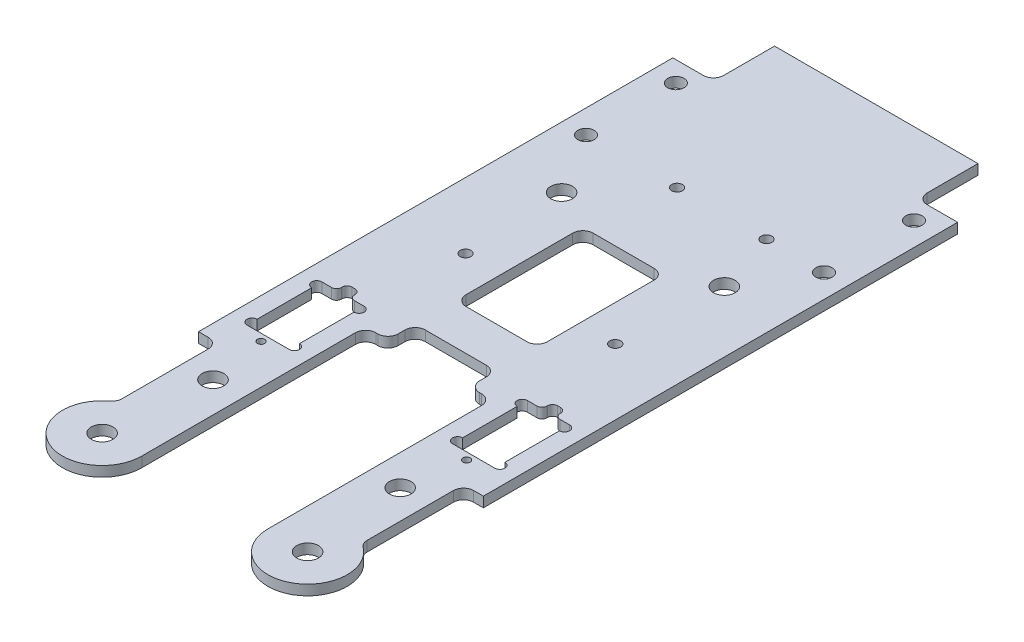
SolidWorks part; units mm, degrees
material "6061-T4 (SS)"
ref_plane "Front Plane" through (0, 0, 0) normal (0, 0, 1) x (1, 0, 0)
ref_plane "Top Plane" through (0, 0, 0) normal (0, 1, 0) x (1, 0, 0)
ref_plane "Right Plane" through (0, 0, 0) normal (1, 0, 0) x (0, 0, -1)
sketch "Sketch1" plane through (0, 0, 0) normal (0, 1, 0) x (1, 0, 0)
  line L1 (-44.45, -114.3) -> (44.45, -114.3)
  line L2 (-44.45, -114.3) -> (-44.45, 114.3)
  line L3 (-44.45, 114.3) -> (44.45, 114.3)
  line L4 (44.45, -114.3) -> (44.45, 114.3)
  line L5 (-44.45, -114.3) -> (44.45, 114.3) construction
  line L6 (-44.45, 114.3) -> (44.45, -114.3) construction
  point P0 (0, 0)
  dimension "D1" = 88.9
  dimension "D2" = 228.6
extrude "Boss-Extrude1" add sketch "Sketch1" along normal blind 3.175
sketch "Sketch11" plane through (0, 3.175, 0) normal (0, 1, 0) x (1, 0, 0)
  line L0 (0, 31.75) -> (97.4414, 31.75) construction
  line L10 (0, 0) -> (0, 114.3) construction
  line L14 (44.45, 114.3) -> (-44.45, 114.3) construction
  line L15 (0, 0) -> (117.475, 0) construction
  circle A0 centre (-26.289, 4.9828) radius 1.25
  circle A1 centre (-25.019, 53.1832) radius 1.25
  circle A2 centre (25.781, 38.1972) radius 1.25
  circle A3 centre (25.781, 10.0628) radius 1.25
  dimension "D3" = 2.5
  dimension "D5" = 2.5
  dimension "D7" = 31.75
  dimension "D9" = 25.781
  dimension "D4" = 2.5
  dimension "D6" = 2.5
  dimension "D2" = 25.019
  dimension "D8" = 26.289
  dimension "D10" = 6.4472
  dimension "D11" = 25.781
  dimension "D12" = 21.6872
  dimension "D13" = 26.7672
  dimension "D14" = 21.4332
extrude "Cut-Extrude12" [suppressed] cut sketch "Sketch11" against normal through all
sketch "Sketch18" plane through (0, 3.175, 0) normal (0, 1, 0) x (1, 0, 0)
  line L0 (44.45, 79.883) -> (-44.45, 79.883) construction
  line L1 (44.45, -114.3) -> (44.45, 114.3) construction
  line L2 (-44.45, 114.3) -> (-44.45, -114.3) construction
  line L3 (44.45, 114.3) -> (-44.45, 114.3) construction
  line L4 (0, 79.883) -> (0, -114.3) construction
  line L5 (-44.45, -114.3) -> (44.45, -114.3) construction
  circle A9 centre (-23.9014, 29.083) radius 1.6891
  circle A10 centre (23.9014, 27.9832) radius 1.6891
  circle A11 centre (-8.702, 79.883) radius 1.6891
  circle A12 centre (19.1999, 79.883) radius 1.6891
  dimension "D4" = 50.8
  dimension "D9" = 15.1994
  dimension "D11" = 3.3782
  dimension "D13" = 43.1013
  dimension "D3" = 3.3782
  dimension "D2" = 3.3782
  dimension "D8" = 3.3782
  dimension "D1" = 34.417
  dimension "D5" = 23.9014
  dimension "D6" = 47.8028
  dimension "D7" = 1.0998
  dimension "D10" = 50.8
  dimension "D12" = 50.8
sketch "Sketch12" plane through (0, 3.175, 0) normal (0, 1, 0) x (1, 0, 0)
  line L0 (0, 0) -> (44.45, 0) construction
  line L1 (44.45, -114.3) -> (44.45, 114.3) construction
  line L2 (0, 0) -> (0, 114.3) construction
  line L3 (44.45, 114.3) -> (-44.45, 114.3) construction
  line L4 (44.45, -44.45) -> (-44.45, -44.45) construction
  line L5 (-19.685, -69.85) -> (19.685, -69.85)
  line L6 (-19.685, -69.85) -> (-19.685, -6.35)
  line L7 (-19.685, -6.35) -> (19.685, -6.35)
  line L8 (19.685, -69.85) -> (19.685, -6.35)
  line L9 (-19.685, -69.85) -> (19.685, -6.35) construction
  line L10 (-19.685, -6.35) -> (19.685, -69.85) construction
  line L11 (-44.45, 114.3) -> (-44.45, -114.3) construction
  line L12 (0, -38.1) -> (0, -114.3) construction
  line L13 (-44.45, -114.3) -> (44.45, -114.3) construction
  circle A0 centre (29.21, -44.45) radius 3.3782
  circle A1 centre (-29.21, -44.45) radius 3.3782
  point P5 (0, -38.1)
  dimension "D5" = 6.7564
  dimension "D1" = 63.5
  dimension "D2" = 38.1
  dimension "D3" = 39.37
  dimension "D4" = 25.4
  dimension "D6" = 58.42
extrude "Cut-Extrude13" cut sketch "Sketch12" against normal through all
sketch "Sketch14" plane through (0, 0, 0) normal (0, -1, 0) x (-1, 0, 0)
  line L0 (0, 114.3) -> (0, 31.056) construction
  line L1 (-44.45, 114.3) -> (44.45, 114.3) construction
  line L2 (0, 114.3) -> (-44.45, 114.3) construction
  line L3 (-41.91, 114.3) -> (-41.91, 67.4804) construction
  line L5 (-32.385, 114.3) -> (-32.385, 67.4804) construction
  line L6 (-32.385, 107.95) -> (-41.91, 107.95) construction
  line L7 (-32.385, 93.9165) -> (-41.91, 93.9165) construction
  line L8 (-44.45, -114.3) -> (-44.45, 114.3) construction
  circle A0 centre (-37.1475, 107.95) radius 2.5527
  circle A1 centre (-37.1475, 79.883) radius 2.5527
  circle A2 centre (37.1475, 107.95) radius 2.5527
  circle A3 centre (37.1475, 79.883) radius 2.5527
  dimension "D4" = 5.1054
  dimension "D1" = 2.54
  dimension "D2" = 9.525
  dimension "D3" = 6.35
  dimension "D5" = 14.0335
extrude "Cut-Extrude15" cut sketch "Sketch14" against normal through all
sketch "Sketch15" plane through (0, 0, 0) normal (0, -1, 0) x (1, 0, 0)
  line L0 (44.45, 114.3) -> (44.45, -114.3) construction
  line L1 (-44.45, 114.3) -> (44.45, 114.3)
  line L2 (-44.45, 114.3) -> (-44.45, 57.15)
  line L3 (-44.45, 57.15) -> (44.45, 57.15)
  line L4 (44.45, 114.3) -> (44.45, 57.15)
  line L5 (19.685, 6.35) -> (-19.685, 6.35) construction
  line L6 (0, -24.0665) -> (0, -114.3) construction
  line L7 (12.7, -51.308) -> (12.7, -17.9917)
  line L8 (9.525, -14.8167) -> (-9.525, -14.8167)
  line L9 (44.45, -114.3) -> (-44.45, -114.3) construction
  line L10 (-12.7, -17.9917) -> (-12.7, -51.308)
  line L11 (9.525, -54.483) -> (-9.525, -54.483)
  line L12 (12.7, -51.308) -> (12.7, 6.35) construction
  line L13 (12.7, 6.35) -> (-12.7, 6.35) construction
  line L14 (-12.7, -51.308) -> (-12.7, 6.35) construction
  line L15 (12.7, -54.483) -> (-12.7, 6.35) construction
  line L16 (12.7, 6.35) -> (-12.7, -54.483) construction
  line L17 (12.7, 6.35) -> (-12.7, 6.35)
  line L18 (-12.7, 6.35) -> (-12.7, 1.0583)
  line L19 (-9.525, -2.1167) -> (9.525, -2.1167)
  line L20 (12.7, 1.0583) -> (12.7, 6.35)
  circle A0 centre (-29.21, 44.45) radius 3.3782 construction
  circle A1 centre (-37.1475, -79.883) radius 2.5527 construction
  arc A2 (-9.525, -54.483) -> (-12.7, -51.308) centre (-9.525, -51.308) cw
  arc A3 (9.525, -54.483) -> (12.7, -51.308) centre (9.525, -51.308) ccw
  arc A4 (12.7, -17.9917) -> (9.525, -14.8167) centre (9.525, -17.9917) ccw
  arc A5 (-9.525, -14.8167) -> (-12.7, -17.9917) centre (-9.525, -17.9917) ccw
  arc A6 (-12.7, 1.0583) -> (-9.525, -2.1167) centre (-9.525, 1.0583) ccw
  arc A7 (9.525, -2.1167) -> (12.7, 1.0583) centre (9.525, 1.0583) ccw
  point P35 (12.7, -14.8167)
  point P38 (-12.7, -14.8167)
  point P41 (-12.7, -2.1167)
  point P44 (12.7, -2.1167)
  dimension "D3" = 3.175
  dimension "D7" = 3.175
  dimension "D1" = 12.7
  dimension "D2" = 25.4
  dimension "D4" = 25.4
  dimension "D5" = 8.4667
  dimension "D6" = 12.7
extrude "Cut-Extrude16" cut sketch "Sketch15" against normal through all
fillet "Fillet1" radius 3.175 4 edges at (19.685, 1.5875, 6.35) (-19.685, 1.5875, 6.35) (-12.7, 1.5875, 6.35) (12.7, 1.5875, 6.35)
extrude "Cut-Extrude18" cut sketch "Sketch18" against normal through all
sketch "Sketch16" plane through (0, 3.175, 0) normal (0, 1, 0) x (1, 0, 0)
  line L0 (44.45, -57.15) -> (44.45, -76.2)
  line L1 (19.685, -57.15) -> (19.685, -76.2)
  line L2 (19.685, -76.2) -> (44.45, -76.2) construction
  line L3 (0, 0) -> (0, -94.827) construction
  line L4 (44.45, -57.15) -> (19.685, -57.15)
  line L5 (-19.685, -57.15) -> (-19.685, -76.2)
  line L6 (-44.45, -57.15) -> (-19.685, -57.15)
  line L7 (-44.45, -57.15) -> (-44.45, -76.2)
  arc A0 (44.45, -76.2) -> (19.685, -76.2) centre (32.0675, -76.2) cw
  arc A1 (-44.45, -76.2) -> (-19.685, -76.2) centre (-32.0675, -76.2) ccw
  circle A2 centre (32.0675, -76.2) radius 3.3782
  circle A3 centre (-32.0675, -76.2) radius 3.3782
  line M12 (-44.45, -57.15) -> (-19.685, -57.15)
  line M16 (19.685, -57.15) -> (44.45, -57.15)
  dimension "D2" = 6.7564
  dimension "D1" = 19.05
extrude "Boss-Extrude2" add sketch "Sketch16" against normal up to surface (3.175 mm away) contours L7 A1 L5 A3 M12 | A0 L0 L1 A2 M16 up to face at (23.9014, 0, -26.2941)
sketch "Sketch19" plane through (0, 3.175, 0) normal (0, 1, 0) x (1, 0, 0)
  line L0 (0, 14.8167) -> (0, 54.483) construction
  line L1 (9.525, 14.8167) -> (-9.525, 14.8167) construction
  line L2 (-9.525, 54.483) -> (9.525, 54.483) construction
  line L4 (-12.7, 17.9917) -> (-12.7, 51.308) construction
  line L6 (-38.1, 53.975) -> (-12.7, 53.975) construction
  line L7 (-25.4, 53.975) -> (-25.4, 60.5367) construction
  line L9 (-44.45, 114.3) -> (-44.45, -76.2) construction
  circle A0 centre (-25.4, 60.5367) radius 3.3782
  circle A1 centre (25.4, 60.5367) radius 3.3782
  dimension "D1" = 6.7564
  dimension "D2" = 45.72
  dimension "D3" = 6.35
extrude "Cut-Extrude19" cut sketch "Sketch19" against normal through all
sketch "Sketch20" plane through (0, 3.175, 0) normal (0, 1, 0) x (1, 0, 0)
  line L0 (0, 0) -> (0, 61.1006) construction
  line L3 (-25.8445, 3.175) -> (-25.8445, -28.575) construction
  line L6 (-25.4635, -1.016) -> (-38.6715, -1.016) construction
  line L7 (-25.4635, -1.016) -> (-25.4635, -24.384) construction
  line L8 (-25.4635, -24.384) -> (-38.6715, -24.384)
  line L9 (-38.6715, -1.016) -> (-38.6715, -24.384) construction
  line L10 (-25.4635, -1.016) -> (-38.6715, -24.384) construction
  line L11 (-25.4635, -24.384) -> (-38.6715, -1.016) construction
  line L13 (-38.2905, 3.175) -> (-38.2905, -28.575) construction
  line L14 (-25.8445, 3.175) -> (-38.2905, -28.575) construction
  line L27 (-32.0675, -76.2) -> (-32.0675, 23.1424) construction
  line L28 (-38.2905, 3.175) -> (-25.8445, -28.575) construction
  line L29 (-38.2905, -28.575) -> (-32.9565, -28.575) construction
  line L30 (-32.9565, -28.575) -> (-32.9565, -27.305) construction
  line L31 (-31.1785, -28.575) -> (-31.1785, -27.305) construction
  line L32 (-25.8445, -28.575) -> (-31.1785, -28.575) construction
  line L33 (-25.8445, 3.175) -> (-31.1785, 3.175) construction
  line L34 (-31.1785, 3.175) -> (-31.1785, 1.905) construction
  line L35 (-32.9565, 3.175) -> (-32.9565, 1.905) construction
  line L36 (-38.2905, 3.175) -> (-32.9565, 3.175) construction
  line L38 (-30.0355, 0.5715) -> (-30.0355, 0.6985)
  line L42 (-28.448, -1.016) -> (-25.4635, -1.016)
  line L44 (-34.0995, 0.5715) -> (-34.0995, 0.6985)
  line L45 (-35.687, -1.016) -> (-38.6715, -1.016)
  line L48 (-32.0675, 1.1866) -> (-32.0675, 0.0436) construction
  line L49 (-32.0675, 1.1866) -> (-32.0675, 0.0436) construction
  line L50 (-32.512, 2.286) -> (-31.623, 2.286)
  line L85 (-25.4635, -4.191) -> (-25.4635, -21.209)
  line L86 (-38.6715, -4.191) -> (-38.6715, -21.209)
  line L87 (25.4635, -24.384) -> (38.6715, -24.384)
  line L88 (25.4635, -4.191) -> (25.4635, -21.209)
  line L89 (28.448, -1.016) -> (25.4635, -1.016)
  line L90 (30.0355, 0.5715) -> (30.0355, 0.6985)
  line L91 (32.512, 2.286) -> (31.623, 2.286)
  line L92 (34.0995, 0.5715) -> (34.0995, 0.6985)
  line L93 (35.687, -1.016) -> (38.6715, -1.016)
  line L94 (38.6715, -4.191) -> (38.6715, -21.209)
  arc A0 (-32.9565, -27.305) -> (-31.1785, -27.305) centre (-32.0675, -26.5866) cw construction
  circle A3 centre (-32.0675, -26.5866) radius 1.143
  arc A9 (-30.0355, 0.6985) -> (-31.623, 2.286) centre (-31.623, 0.6985) ccw
  arc A10 (-32.512, 2.286) -> (-34.0995, 0.6985) centre (-32.512, 0.6985) ccw
  arc A16 (-30.0355, 0.5715) -> (-28.448, -1.016) centre (-28.448, 0.5715) ccw
  arc A17 (-34.0995, 0.5715) -> (-35.687, -1.016) centre (-35.687, 0.5715) cw
  arc A23 (-25.4635, -24.384) -> (-25.4635, -21.209) centre (-25.4635, -22.7965) ccw
  arc A24 (-25.4635, -1.016) -> (-25.4635, -4.191) centre (-25.4635, -2.6035) cw
  arc A25 (-38.6715, -24.384) -> (-38.6715, -21.209) centre (-38.6715, -22.7965) cw
  arc A26 (-38.6715, -1.016) -> (-38.6715, -4.191) centre (-38.6715, -2.6035) ccw
  circle A27 centre (32.0675, -26.5866) radius 1.143
  arc A28 (25.4635, -24.384) -> (25.4635, -21.209) centre (25.4635, -22.7965) cw
  arc A29 (25.4635, -1.016) -> (25.4635, -4.191) centre (25.4635, -2.6035) ccw
  arc A30 (30.0355, 0.5715) -> (28.448, -1.016) centre (28.448, 0.5715) cw
  arc A31 (30.0355, 0.6985) -> (31.623, 2.286) centre (31.623, 0.6985) cw
  arc A32 (32.512, 2.286) -> (34.0995, 0.6985) centre (32.512, 0.6985) cw
  arc A33 (34.0995, 0.5715) -> (35.687, -1.016) centre (35.687, 0.5715) ccw
  arc A34 (38.6715, -1.016) -> (38.6715, -4.191) centre (38.6715, -2.6035) cw
  arc A35 (38.6715, -24.384) -> (38.6715, -21.209) centre (38.6715, -22.7965) ccw
  point P10 (-32.0675, -12.7)
  point P16 (-32.0675, -12.7)
  point P38 (-30.0355, 2.286)
  point P45 (-34.0995, 2.286)
  point P54 (-30.0355, -1.016)
  point P57 (-34.0995, -1.016)
  dimension "D6" = 1.5875
  dimension "D7" = 1.5875
  dimension "D8" = 1.5875
  dimension "D9" = 1.5875
  dimension "D1" = 13.208
  dimension "D2" = 23.368
  dimension "D3" = 63.5
  dimension "D4" = 2.032
  dimension "D5" = 3.302
extrude "Cut-Extrude20" cut sketch "Sketch20" against normal through all
sketch "Sketch21" plane through (0, 0, -114.3) normal (0, 0, -1) x (-1, 0, 0)
  line L1 (44.45, 0) -> (-44.45, 0)
  line L2 (44.45, 0) -> (44.45, 3.175)
  line L3 (44.45, 3.175) -> (-44.45, 3.175)
  line L4 (-44.45, 0) -> (-44.45, 3.175)
extrude "Boss-Extrude3" add sketch "Sketch21" along normal blind 19.05
sketch "Sketch22" plane through (0, 3.175, 0) normal (0, 1, 0) x (1, 0, 0)
  line L0 (0, 54.483) -> (0, 133.35) construction
  line L1 (-44.45, 133.35) -> (-31.75, 133.35)
  line L2 (-44.45, 133.35) -> (-44.45, 114.3)
  line L3 (-44.45, 114.3) -> (-34.925, 114.3)
  line L4 (-31.75, 133.35) -> (-31.75, 117.475)
  line L5 (-9.525, 54.483) -> (9.525, 54.483) construction
  line L6 (44.45, 133.35) -> (-44.45, 133.35) construction
  line L7 (44.45, 114.3) -> (34.925, 114.3)
  line L8 (31.75, 133.35) -> (31.75, 117.475)
  line L9 (44.45, 133.35) -> (31.75, 133.35)
  line L10 (44.45, 133.35) -> (44.45, 114.3)
  arc A0 (-34.925, 114.3) -> (-31.75, 117.475) centre (-34.925, 117.475) ccw
  arc A1 (34.925, 114.3) -> (31.75, 117.475) centre (34.925, 117.475) cw
  point P13 (-31.75, 114.3)
  dimension "D3" = 3.175
  dimension "D1" = 12.7
  dimension "D2" = 19.05
extrude "Cut-Extrude21" cut sketch "Sketch22" against normal through all
sketch "Sketch23" plane through (0, 3.175, 0) normal (0, 1, 0) x (1, 0, 0)
  line L0 (-38.2587, -63.7779) -> (-38.2587, -36.9014)
  line L1 (-41.4337, -33.7264) -> (-44.45, -33.7264)
  line L2 (-44.45, 114.3) -> (-44.45, -76.2) construction
  line L3 (-44.45, -33.7264) -> (-44.45, -76.2)
  line L4 (0, 0) -> (0, -80.0101) construction
  line L5 (41.4337, -33.7264) -> (44.45, -33.7264)
  line L6 (38.2587, -63.7779) -> (38.2587, -36.9014)
  line L7 (44.45, -33.7264) -> (44.45, -76.2)
  circle A0 centre (-32.0675, -76.2) radius 12.3825 construction
  arc A1 (-44.45, -76.2) -> (-39.5223, -66.313) centre (-32.0675, -76.2) cw
  arc A2 (-39.5223, -66.313) -> (-38.2587, -63.7779) centre (-41.4337, -63.7779) ccw
  arc A3 (-38.2587, -36.9014) -> (-41.4337, -33.7264) centre (-41.4337, -36.9014) ccw
  arc A4 (38.2587, -36.9014) -> (41.4337, -33.7264) centre (41.4337, -36.9014) cw
  arc A5 (39.5223, -66.313) -> (38.2587, -63.7779) centre (41.4337, -63.7779) cw
  arc A6 (44.45, -76.2) -> (39.5223, -66.313) centre (32.0675, -76.2) ccw
  point P12 (-38.2587, -65.4764)
  point P15 (-38.2587, -33.7264)
  dimension "D1" = 60
  dimension "D3" = 3.175
  dimension "D2" = 31.75
extrude "Cut-Extrude22" cut sketch "Sketch23" against normal through all
